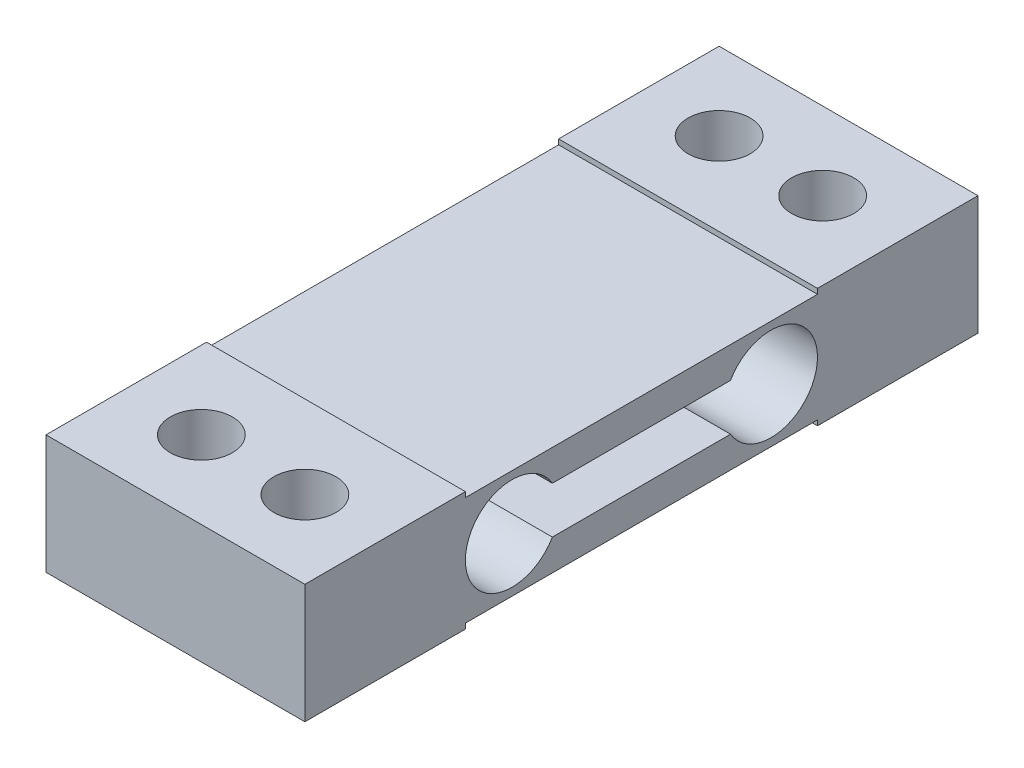
SolidWorks part; units mm, degrees
material "3003 Alloy"
ref_plane "Front Plane" through (0, 0, 0) normal (0, 0, 1) x (1, 0, 0)
ref_plane "Top Plane" through (0, 0, 0) normal (0, 1, 0) x (1, 0, 0)
ref_plane "Right Plane" through (0, 0, 0) normal (1, 0, 0) x (0, 0, -1)
sketch "Sketch2" plane through (0, 0, 0) normal (1, 0, 0) x (0, 0, -1)
  line L1 (0, 0) -> (130, 0)
  line L2 (0, 0) -> (0, 23)
  line L3 (0, 23) -> (130, 23)
  line L4 (130, 0) -> (130, 23)
  line L7 (82.2058, 16) -> (47.7942, 16)
  line L10 (82.2058, 7) -> (47.7942, 7)
  arc A0 (82.2058, 7) -> (82.2058, 16) centre (90, 11.5) ccw
  arc A1 (47.7942, 7) -> (47.7942, 16) centre (40, 11.5) cw
extrude "Boss-Extrude1" add sketch "Sketch2" along normal blind 50
sketch "Sketch3" plane through (0, 23, 0) normal (0, 1, 0) x (1, 0, 0)
  circle A0 centre (15, 15) radius 6
  circle A1 centre (35, 15) radius 6
  circle A2 centre (15, 115) radius 6
  circle A3 centre (35, 115) radius 6
extrude "Cut-Extrude1" cut sketch "Sketch3" against normal blind 23
sketch "Sketch4" plane through (0, 23, 0) normal (0, 1, 0) x (1, 0, 0)
  line L0 (50, 130) -> (50, 0) construction
  line L3 (0, 99) -> (50, 99)
  line L5 (0, 99) -> (0, 31)
  line L8 (0, 31) -> (50, 31)
  line L10 (50, 99) -> (50, 31)
  line L11 (0, 99) -> (0, 31)
  line M13 (0, 130) -> (0, 0)
  line M15 (50, 0) -> (50, 130)
extrude "Cut-Extrude3" cut sketch "Sketch4" against normal blind 1 contours L8 L3 M13 M15
sketch "Sketch5" plane through (0, 0, 0) normal (0, -1, 0) x (1, 0, 0)
  line L0 (50, 0) -> (50, -130) construction
  line L3 (0, -31) -> (50, -31)
  line L5 (0, -31) -> (0, -99)
  line L8 (0, -99) -> (50, -99)
  line L10 (50, -31) -> (50, -99)
extrude "Cut-Extrude4" cut sketch "Sketch5" against normal blind 1
